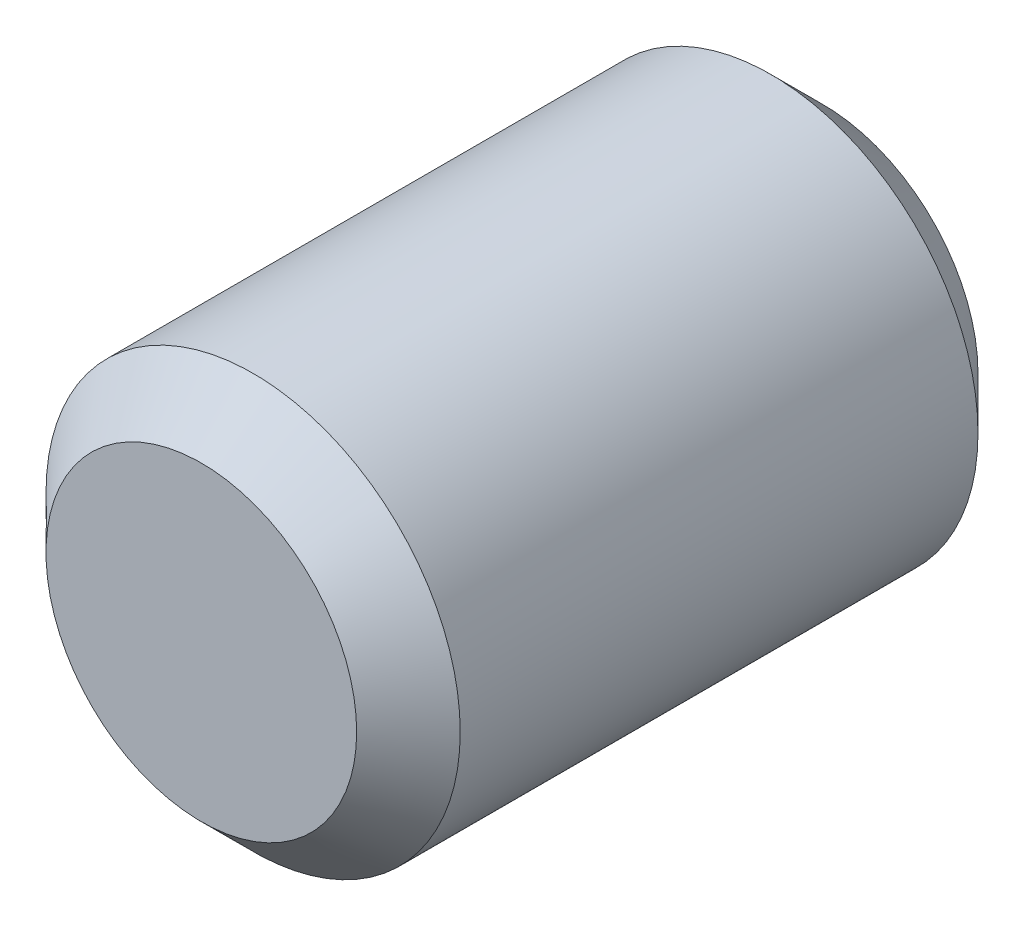
SolidWorks part; units mm, degrees
ref_plane "Front Plane" through (0, 0, 0) normal (0, 0, 1) x (1, 0, 0)
ref_plane "Top Plane" through (0, 0, 0) normal (0, 1, 0) x (1, 0, 0)
ref_plane "Right Plane" through (0, 0, 0) normal (1, 0, 0) x (0, 0, -1)
sketch "Sketch1" plane through (0, 0, 0) normal (0, 0, 1) x (1, 0, 0)
  circle A0 centre (0, 0) radius 2
  dimension "D1" = 4
extrude "Boss-Extrude1" add sketch "Sketch1" along normal blind 6
chamfer "Chamfer1" distance 0.5 angle 45 2 edges at (2, 0, 0) (2, 0, 6)
